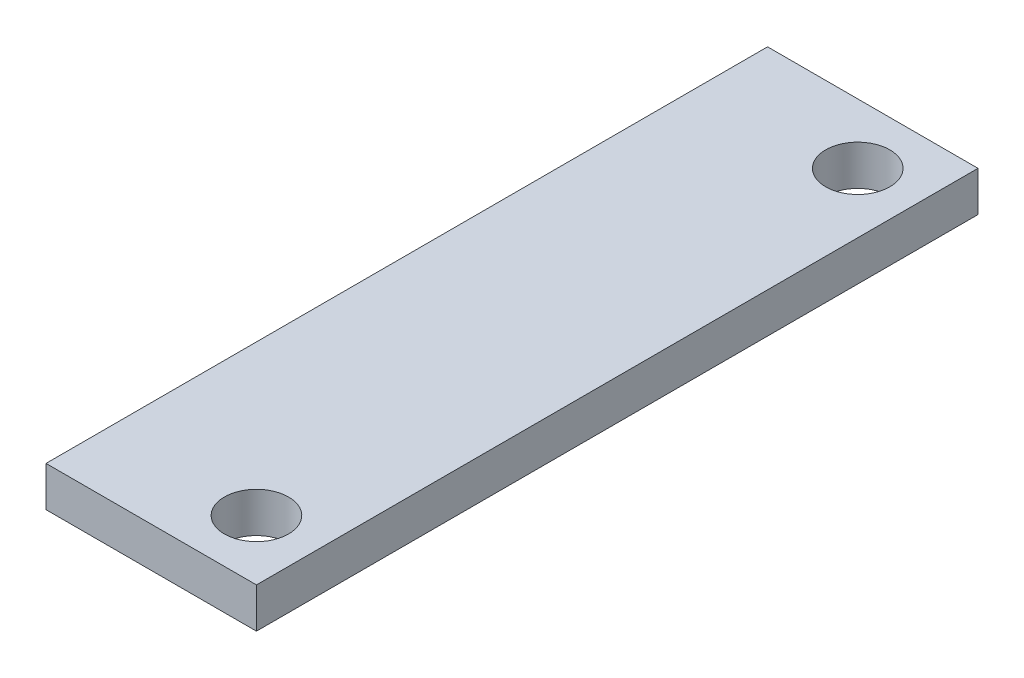
SolidWorks part; units mm, degrees
ref_plane "前视基准面" through (0, 0, 0) normal (0, 0, 1) x (1, 0, 0)
ref_plane "上视基准面" through (0, 0, 0) normal (0, 1, 0) x (1, 0, 0)
ref_plane "右视基准面" through (0, 0, 0) normal (1, 0, 0) x (0, 0, -1)
sketch "草图1" plane through (0, 0, 0) normal (0, 1, 0) x (1, 0, 0)
  line L1 (0, 0) -> (10.5, 0)
  line L2 (0, 0) -> (0, 36)
  line L3 (0, 36) -> (10.5, 36)
  line L4 (10.5, 0) -> (10.5, 36)
  dimension "D1" = 36
  dimension "D2" = 10.5
extrude "凸台-拉伸1" add sketch "草图1" along normal blind 2
sketch "草图2" plane through (0, 0, 0) normal (0, -1, 0) x (-1, 0, 0)
  line L0 (-10.5, 0) -> (-10.5, 36) construction
  circle A0 centre (-7.5, 33) radius 1.6
  circle A1 centre (-7.5, 3) radius 1.6
  dimension "D1" = 3.2
  dimension "D2" = 30
  dimension "D3" = 3
extrude "切除-拉伸1" cut sketch "草图2" against normal through all
sketch "草图3" plane through (0, 0, 0) normal (0, -1, 0) x (-1, 0, 0)
  line L0 (0, 18) -> (-0.75, 18) construction
  line L1 (-0.75, 30.5) -> (-9.75, 30.5)
  line L2 (-0.75, 30.5) -> (-0.75, 5.5)
  line L3 (-0.75, 5.5) -> (-9.75, 5.5)
  line L4 (-9.75, 30.5) -> (-9.75, 5.5)
  line L5 (0, 36) -> (0, 0) construction
  line L6 (-5.25, 30.5) -> (-5.25, 36) construction
  line L7 (-10.5, 36) -> (0, 36) construction
  dimension "D1" = 9
  dimension "D2" = 25
extrude "切除-拉伸2" cut sketch "草图3" against normal blind 1
sketch "草图6" plane through (0, 0, 0) normal (0, -1, 0) x (-1, 0, 0)
  line L0 (-0.75, 5.5) -> (-0.75, 30.5) construction
  line L1 (-0.75, 18) -> (0, 18)
  line L2 (-0.75, 18) -> (-0.75, 17)
  line L3 (-0.75, 17) -> (0, 17)
  line L4 (0, 18) -> (0, 17)
  line L5 (0, 36) -> (0, 0) construction
  dimension "D1" = 1
extrude "切除-拉伸3" cut sketch "草图6" against normal blind 0.5
sketch "草图7" plane through (0, 0, 0) normal (0, -1, 0) x (-1, 0, 0)
  line L0 (-10.5, 36) -> (0, 36) construction
  line L1 (-1, 36) -> (-5.3, 36)
  line L2 (-1, 36) -> (-1, 30.5)
  line L3 (-1, 30.5) -> (-5.3, 30.5)
  line L4 (-5.3, 36) -> (-5.3, 30.5)
  line L5 (-0.75, 30.5) -> (-9.75, 30.5) construction
  line L6 (-3.15, 30.5) -> (-3.15, 20.6902) construction
  line L7 (-0.75, 18) -> (-0.75, 30.5) construction
  dimension "D1" = 4.3
  dimension "D2" = 2.4
extrude "切除-拉伸4" cut sketch "草图7" against normal blind 0.2
